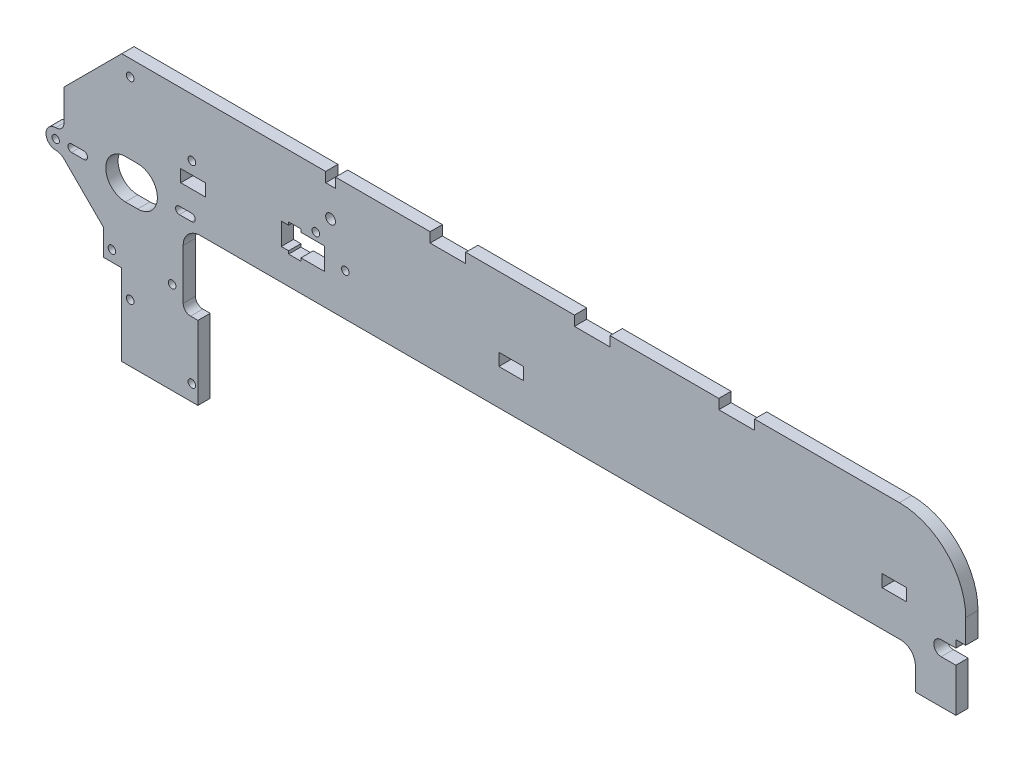
SolidWorks part; units mm, degrees
material "6061-T6 Black anodised"
ref_plane "Front Plane" through (0, 0, 0) normal (0, 0, 1) x (1, 0, 0)
ref_plane "Top Plane" through (0, 0, 0) normal (0, 1, 0) x (1, 0, 0)
ref_plane "Right Plane" through (0, 0, 0) normal (1, 0, 0) x (0, 0, -1)
sketch "Sketch1" plane through (0, 0, 0) normal (0, 0, 1) x (1, 0, 0)
  line L0 (-19.5, 0) -> (36.1968, 0) construction
  line L1 (-1.5, 32) -> (20.5, 32) construction
  line L2 (-21.9203, 0) -> (-30, 0) construction
  line L3 (-6.5, 43.5) -> (-6.5, 28.8553) construction
  line L4 (-1.5, 43.5) -> (20.5, 43.5) construction
  line L5 (310, 43.5) -> (251, 43.5)
  line L6 (21.9203, 0) -> (0, 21.9203) construction
  line L7 (0, 21.9203) -> (-21.9203, 0) construction
  line L8 (-21.9203, 0) -> (0, -21.9203) construction
  line L9 (0, -21.9203) -> (21.9203, 0) construction
  line L10 (316.5, -4.6) -> (316.5, -20)
  line L11 (-6.5, -65) -> (-6.5, -32)
  line L12 (-30, 5.3553) -> (-30, -5.3553) construction
  line L13 (327, 3.7) -> (333, 3.7)
  line L14 (316.5, -20) -> (333, -20)
  line L15 (18.5, -4.6) -> (316.5, -4.6)
  line L16 (34.5, -11.1) -> (59.432, -11.1) construction
  line L17 (333, 6.7) -> (333, 3.7)
  line L18 (9.5, 43.5) -> (9.5, -35.4767) construction
  line L19 (-1.5, 43.5) -> (20.5, 43.5) construction
  line L20 (-1.5, 43.5) -> (-1.5, 20.5) construction
  line L21 (-6.5, -65) -> (24.5, -65)
  line L22 (-1.5, 20.5) -> (20.5, 20.5) construction
  line L23 (327, -2.3) -> (333, -2.3)
  line L24 (333, -2.3) -> (333, -20)
  line L25 (333, 6.7) -> (337, 6.7)
  line L26 (337, 6.7) -> (337, 16.5)
  line L27 (18.5, -35) -> (18.5, -4.6)
  line L28 (20.5, 43.5) -> (20.5, 20.5) construction
  line L29 (17.5, 15) -> (17.5, 10)
  line L30 (17.5, 15) -> (27.5, 15)
  line L31 (27, 72.5933) -> (67, 72.5933) construction
  line L32 (147, 10) -> (157, 10)
  line L33 (147, 10) -> (147, 15)
  line L34 (17.5, 10) -> (27.5, 10)
  line L35 (27.5, 15) -> (27.5, 10)
  line L36 (147, 15) -> (157, 15)
  line L37 (157, 10) -> (157, 15)
  line L38 (303, 10) -> (313, 10)
  line L39 (303, 10) -> (303, 15)
  line L40 (303, 15) -> (313, 15)
  line L41 (313, 10) -> (313, 15)
  line L42 (27, 72.5933) -> (27, -81.6129) construction
  line L43 (27, -81.6129) -> (67, -81.6129) construction
  line L44 (67, 72.5933) -> (67, -81.6129) construction
  line L45 (-1.5, -52.5) -> (20.5, -52.5) construction
  line L46 (-1.5, -65) -> (20.5, -65) construction
  line L47 (-1.5, -65) -> (-1.5, -42) construction
  line L48 (-1.5, -42) -> (20.5, -42) construction
  line L49 (20.5, -65) -> (20.5, -42) construction
  line L50 (58.4277, 8) -> (61.4277, 8)
  line L51 (27.5, 12.5) -> (63.9277, 12.5) construction
  line L52 (61.4277, 6.8061) -> (66.4277, 6.8061)
  line L53 (61.4277, 6.8061) -> (61.4277, 8)
  line L54 (76, 8) -> (76, 17)
  line L55 (72.5, 20.1) -> (72.5, 7.1) construction
  line L56 (66.4277, 6.8061) -> (66.4277, 8)
  line L57 (66.4277, 8) -> (76, 8)
  line L58 (63.9277, 12.5) -> (76, 12.5) construction
  line L59 (66.4277, 18.1939) -> (61.4277, 18.1939)
  line L60 (66.4277, 6.8061) -> (61.4277, 18.1939) construction
  line L61 (61.4277, 6.8061) -> (66.4277, 18.1939) construction
  line L62 (18.5, -35) -> (24.5, -35)
  line L63 (66.4277, 17) -> (66.4277, 18.1939)
  line L64 (66.4277, 17) -> (76, 17)
  line L65 (61.4277, 17) -> (61.4277, 18.1939)
  line L66 (24.5, -35) -> (24.5, -65)
  line L67 (-14, -21.3553) -> (-30, -5.3553)
  line L68 (-14, -21.3553) -> (-14, -32)
  line L69 (-14, -32) -> (-6.5, -32)
  line L70 (119, 43.5) -> (119, 39.5)
  line L71 (119, 39.5) -> (133.5, 39.5)
  line L72 (177.75, 43.5) -> (177.75, 39.5)
  line L73 (119, 43.5) -> (80.5, 43.5)
  line L74 (-6.5, 28.8553) -> (-30, 5.3553) construction
  line L75 (177.75, 39.5) -> (192.25, 39.5)
  line L76 (159.788, -14) -> (-14, -14) construction
  line L77 (159.788, -14) -> (159.788, -26) construction
  line L78 (61.4277, 17) -> (58.4277, 17)
  line L79 (159.788, -26) -> (-14, -26) construction
  line L80 (-14, -14) -> (-14, -26) construction
  line L81 (58.4277, 17) -> (58.4277, 8)
  line L82 (159.788, -14) -> (-14, -26) construction
  line L83 (159.788, -26) -> (-14, -14) construction
  line L84 (192.25, 39.5) -> (192.25, 43.5)
  line L86 (236.5, 43.5) -> (236.5, 39.5)
  line L87 (236.5, 39.5) -> (251, 39.5)
  line L88 (251, 39.5) -> (251, 43.5)
  line L89 (177.75, 43.5) -> (133.5, 43.5)
  line L91 (-33.3631, 8.7185) -> (-33.3631, -8.7185) construction
  line L92 (76.5, 27.7514) -> (80.5, 27.7514) construction
  line L93 (133.5, 39.5) -> (133.5, 43.5)
  line L94 (76.5, 43.5) -> (76.5, 39.5)
  line L95 (76.5, 39.5) -> (80.5, 39.5)
  line L96 (80.5, 43.5) -> (80.5, 39.5)
  line L97 (76.5, 43.5) -> (-6.5, 43.5)
  line L98 (-30, 20) -> (-6.5, 43.5)
  line L99 (-30, 20) -> (-30, 7.3254)
  line L101 (119, 43.5) -> (177.75, 43.5) construction
  line L102 (192.25, 43.5) -> (236.5, 43.5)
  circle A0 centre (9.5, 34.5) radius 1.55 construction
  circle A1 centre (0, 0) radius 15.5 construction
  circle A2 centre (0, 21.9203) radius 1.5 construction
  circle A3 centre (21.9203, 0) radius 1.5
  circle A4 centre (0, -21.9203) radius 1.5 construction
  circle A5 centre (-21.9203, 0) radius 1.5
  circle A6 centre (0, 0) radius 5.5 construction
  arc A7 (337, 16.5) -> (310, 43.5) centre (310, 16.5) ccw
  circle A8 centre (0, 0) radius 8
  circle A9 centre (-3.05, 37) radius 1.55
  circle A10 centre (9.5, -57) radius 1.55 construction
  arc A11 (327, 3.7) -> (327, -2.3) centre (327, 0.7) ccw
  circle A12 centre (72, 0.4) radius 5 construction
  circle A13 centre (22, 38.5) radius 5 construction
  circle A14 centre (22, 38.5) radius 1.5 construction
  circle A15 centre (72, 0.4) radius 1.5 construction
  circle A16 centre (22.05, 20) radius 1.55
  circle A17 centre (-3.05, -41.5) radius 1.55
  circle A18 centre (22.05, -58.5) radius 1.55
  circle A19 centre (81.5, 20.1) radius 1.55 construction
  circle A20 centre (72.5, 20.1) radius 1.55
  circle A21 centre (84.5, 12.5) radius 1.55
  circle A22 centre (-10.5, -27.55) radius 1.55
  arc A23 (-33.3631, 3.9623) -> (-33.3631, -3.9623) centre (-33.3631, 0) ccw
  circle A24 centre (14, -27.55) radius 1.55
  circle A25 centre (-33.3631, 0) radius 1.5
  arc A26 (-33.3631, 3.9623) -> (-30, 7.3254) centre (-33.3631, 7.3254) ccw
  arc A27 (-33.3631, -3.9623) -> (-30, -5.3553) centre (-33.3631, -8.7185) cw
  circle A28 centre (78.5, 27.7514) radius 2
  point P18 (26.8692, -2.8293)
  point P19 (26.8692, 2.8293)
  point P108 (58.4277, 12.5)
  point P115 (72.894, -20)
  dimension "D2" = 31
  dimension "D3" = 3
  dimension "D4" = 11
  dimension "D12" = 16
  dimension "D20" = 3.1
  dimension "D22" = 8
  dimension "D25" = 3
  dimension "D28" = 6
  dimension "D32" = 10
  dimension "D38" = 3
  dimension "D14" = 31
  dimension "D41" = 3.1
  dimension "D44" = 9
  dimension "D45" = 3.1
  dimension "D53" = 6
  dimension "D18" = 7.5
  dimension "D57" = 3.1
  dimension "D69" = 4
  dimension "D7" = 9
  dimension "D11" = 16.5
  dimension "D17" = 15
  dimension "D8" = 65
  dimension "D9" = 43.5
  dimension "D5" = 9.5
  dimension "D6" = 4.6
  dimension "D10" = 6.5
  dimension "D13" = 337
  dimension "D15" = 23
  dimension "D16" = 25
  dimension "D19" = 30
  dimension "D21" = 9
  dimension "D23" = 21.1
  dimension "D24" = 15.4
  dimension "D26" = 6
  dimension "D27" = 4
  dimension "D29" = 67
  dimension "D30" = 17.5
  dimension "D31" = 40
  dimension "D33" = 5
  dimension "D34" = 10
  dimension "D35" = 24
  dimension "D36" = 180
  dimension "D37" = 22
  dimension "D39" = 5
  dimension "D40" = 12
  dimension "D42" = 11
  dimension "D43" = 6
  dimension "D46" = 3.1
  dimension "D47" = 9
  dimension "D48" = 15
  dimension "D49" = 0.7
  dimension "D50" = 5
  dimension "D51" = 12
  dimension "D52" = 3.5
  dimension "D54" = 4
  dimension "D55" = 12
  dimension "D56" = 20
  dimension "D58" = 4.5
  dimension "D59" = 3
  dimension "D60" = 9
  dimension "D61" = 30
  dimension "D62" = 12.5
  dimension "D63" = 52
  dimension "D64" = 14.5
  dimension "D68" = 4
  dimension "D70" = 6
  dimension "D72" = 58.75
  dimension "D67" = 3
extrude "Boss-Extrude1" add sketch "Sketch1" along normal blind 5
fillet "Fillet1" [suppressed] radius 8
fillet "Fillet2" radius 7 1 edges at (18.5, -4.6, 2.5)
fillet "Fillet3" radius 3 1 edges at (18.5, -35, 2.5)
sketch "Sketch2" plane through (0, 0, 5) normal (0, 0, 1) x (1, 0, 0)
  line L0 (21.9203, 0) -> (16.9203, 0) construction
  line L1 (21.9203, -1.5) -> (16.9203, -1.5)
  line L2 (21.9203, 1.5) -> (16.9203, 1.5)
  line L3 (0, 0) -> (-5, 0) construction
  line L4 (0, -8) -> (-5, -8)
  line L5 (0, 8) -> (-5, 8)
  line L6 (-21.9203, 0) -> (-26.9203, 0) construction
  line L7 (-21.9203, -1.5) -> (-26.9203, -1.5)
  line L8 (-21.9203, 1.5) -> (-26.9203, 1.5)
  arc A0 (21.9203, -1.5) -> (21.9203, 1.5) centre (21.9203, 0) ccw
  arc A1 (16.9203, 1.5) -> (16.9203, -1.5) centre (16.9203, 0) ccw
  arc A2 (0, -8) -> (0, 8) centre (0, 0) ccw
  arc A3 (-5, 8) -> (-5, -8) centre (-5, 0) ccw
  arc A4 (-21.9203, -1.5) -> (-21.9203, 1.5) centre (-21.9203, 0) ccw
  arc A5 (-26.9203, 1.5) -> (-26.9203, -1.5) centre (-26.9203, 0) ccw
  circle A6 centre (21.9203, 0) radius 1.5 construction
  circle A7 centre (0, 0) radius 8 construction
  point P4 (19.4203, 0)
  point P9 (-2.5, 0)
  point P16 (-24.4203, 0)
  dimension "D1" = 5
extrude "Cut-Extrude1" cut sketch "Sketch2" against normal through all
fillet "Fillet4" radius 6 1 edges at (316.5, -4.6, 2.5)
sketch "Sketch3" plane through (0, 0, 5) normal (0, 0, 1) x (1, 0, 0)
  line L0 (-12.375, 32.625) -> (-12.375, 37.625) construction
  line L1 (-13.125, 42.8359) -> (-11.625, 42.8359)
  line L2 (-13.125, 42.8359) -> (-13.125, 33.924)
  line L3 (-6.5, 43.5) -> (-30, 20) construction
  line L4 (-11.625, 42.8359) -> (-11.625, 33.924)
  line L5 (-13.125, 42.8359) -> (-11.625, 33.924) construction
  line L6 (-13.125, 33.924) -> (-11.625, 42.8359) construction
  line L7 (-6.5, 43.5) -> (-12.375, 37.625) construction
  line L8 (-12.375, 37.625) -> (-18.25, 31.75) construction
  line L9 (-18.25, 31.75) -> (-24.125, 25.875) construction
  line L10 (-24.125, 25.875) -> (-30, 20) construction
  line L11 (-17.4, 36.9218) -> (-17.4, 27.9859)
  line L12 (-18.25, 26.75) -> (-18.25, 31.75) construction
  line L13 (-19.1, 36.9218) -> (-17.4, 27.9859) construction
  line L14 (-19.1, 27.9859) -> (-17.4, 36.9218) construction
  line L15 (-19.1, 36.9218) -> (-19.1, 27.9859)
  line L16 (-19.1, 36.9218) -> (-17.4, 36.9218)
  line L17 (-23.275, 31.0468) -> (-23.275, 22.1109)
  line L18 (-24.975, 31.0468) -> (-23.275, 22.1109) construction
  line L19 (-24.975, 22.1109) -> (-23.275, 31.0468) construction
  line L20 (-24.975, 31.0468) -> (-23.275, 31.0468)
  line L21 (-24.125, 20.875) -> (-24.125, 25.875) construction
  line L22 (-24.975, 31.0468) -> (-24.975, 22.1109)
  arc A0 (-13.125, 33.924) -> (-11.625, 33.924) centre (-12.375, 32.625) ccw
  arc A1 (-19.1, 27.9859) -> (-17.4, 27.9859) centre (-18.25, 26.75) ccw
  arc A2 (-24.975, 22.1109) -> (-23.275, 22.1109) centre (-24.125, 20.875) ccw
  point P0 (-12.375, 38.3799)
  point P15 (-18.25, 32.4539)
  point P22 (-24.125, 26.5789)
  dimension "D1" = 1.5
  dimension "D2" = 1.5
  dimension "D3" = 5
extrude "Cut-Extrude2" [suppressed] cut sketch "Sketch3" against normal through all
fillet "Fillet5" [suppressed] radius 0.5
equation "\"y-plate-thickness\"=5"
equation "\"bed-plate-thickness\"=6"
equation "\"x-plate-thickness\"=5"
equation "\"D1@Boss-Extrude1\"=\"x-plate-thickness\""
equation "\"D33@Sketch1\"=\"x-plate-thickness\""
